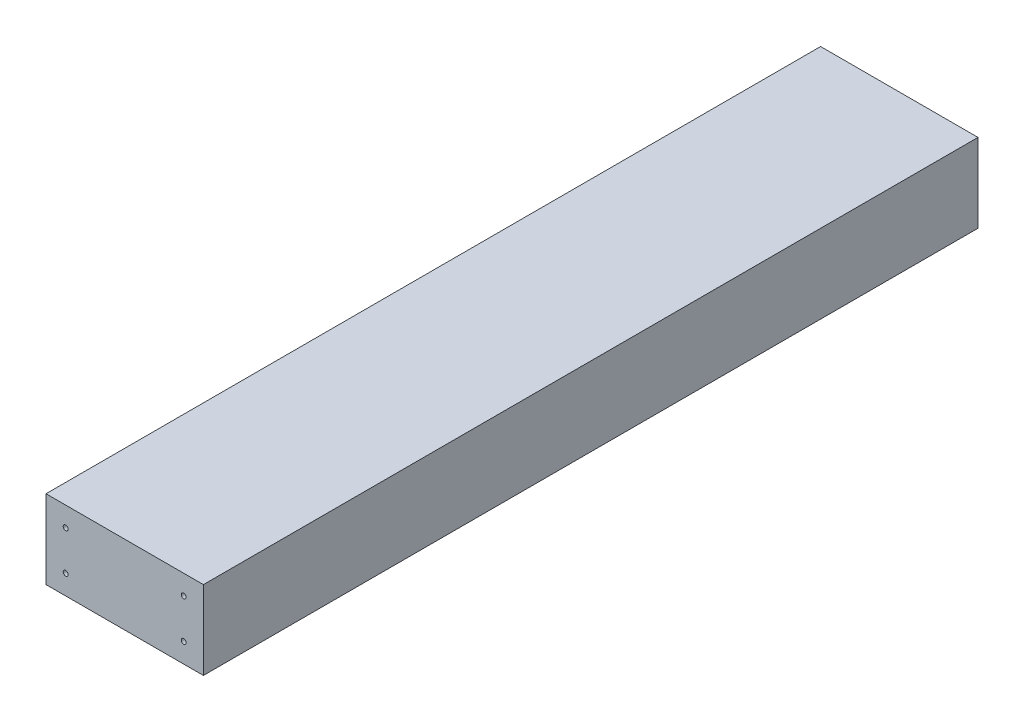
SolidWorks part; units mm, degrees
material "Pine"
ref_plane "Front Plane" through (0, 0, 0) normal (0, 0, 1) x (1, 0, 0)
ref_plane "Top Plane" through (0, 0, 0) normal (0, 1, 0) x (1, 0, 0)
ref_plane "Right Plane" through (0, 0, 0) normal (1, 0, 0) x (0, 0, -1)
sketch "Sketch1" plane through (0, 0, 0) normal (0, 0, 1) x (1, 0, 0)
  line L1 (-50.8, -25.4) -> (50.8, -25.4)
  line L2 (-50.8, -25.4) -> (-50.8, 25.4)
  line L3 (-50.8, 25.4) -> (50.8, 25.4)
  line L4 (50.8, -25.4) -> (50.8, 25.4)
  line L5 (-50.8, -25.4) -> (50.8, 25.4) construction
  line L6 (-50.8, 25.4) -> (50.8, -25.4) construction
  point P0 (0, 0)
  dimension "D1" = 50.8
  dimension "D2" = 101.6
extrude "Boss-Extrude1" add sketch "Sketch1" along normal blind 500
sketch "Sketch2" plane through (0, 0, 500) normal (0, 0, 1) x (1, 0, 0)
  line L0 (-50.8, 25.4) -> (-50.8, -25.4) construction
  line L1 (50.8, -25.4) -> (50.8, 25.4) construction
  line L2 (-38.1, -12.7) -> (-38.1, 12.7) construction
  line L3 (50.8, 25.4) -> (-50.8, 25.4) construction
  line L4 (38.1, 12.7) -> (-38.1, 12.7) construction
  line L5 (-38.1, -12.7) -> (38.1, -12.7) construction
  line L6 (38.1, -12.7) -> (38.1, 12.7) construction
  line L7 (-50.8, -25.4) -> (50.8, -25.4) construction
  circle A2 centre (-38.1, 12.7) radius 1.5875
  circle A3 centre (38.1, 12.7) radius 1.5875
  circle A4 centre (38.1, -12.7) radius 1.5875
  circle A5 centre (-38.1, -12.7) radius 1.5875
  dimension "D1" = 12.7
  dimension "D2" = 12.7
  dimension "D3" = 3.175
  dimension "D4" = 12.7
  dimension "D5" = 12.7
  dimension "D6" = 25.4
extrude "Cut-Extrude1" cut sketch "Sketch2" against normal blind 44.45
ref_plane "Plane1" through (0, 0, 250) normal (0, 0, -1) x (-1, 0, 0)
mirror "Mirror1" about plane through (0, 0, 250) normal (0, 0, -1) of "Cut-Extrude1"
